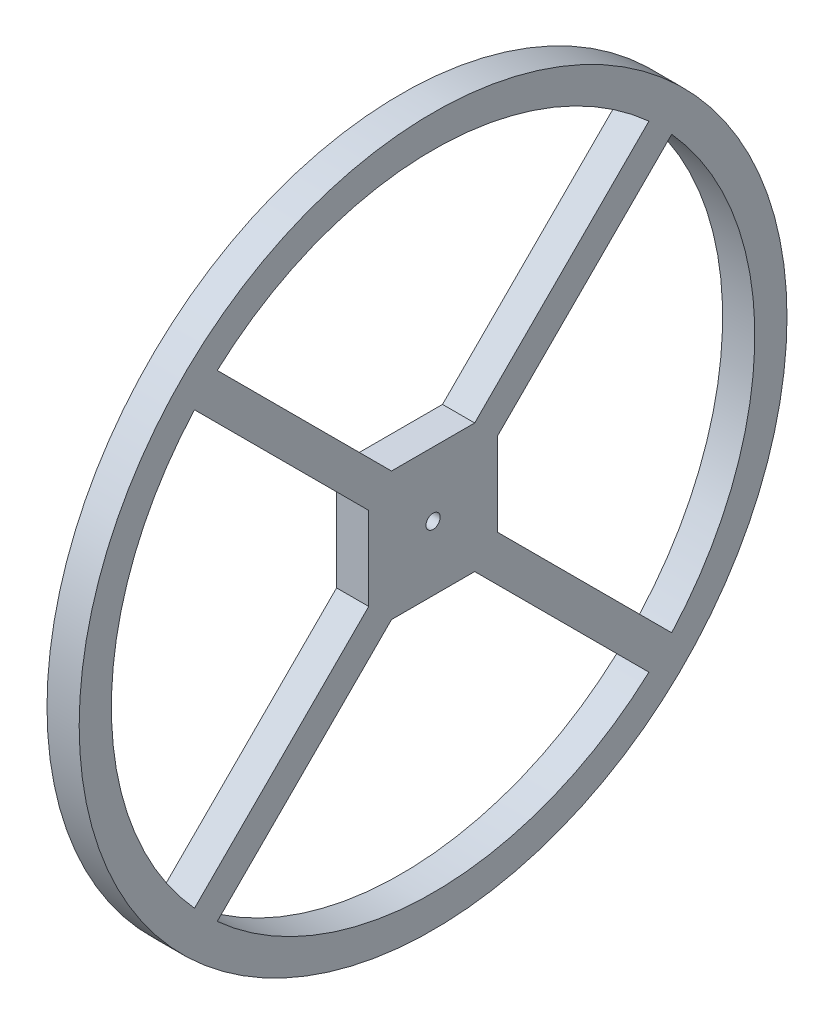
SolidWorks part; units mm, degrees
ref_plane "Front Plane" through (0, 0, 0) normal (0, 0, 1) x (1, 0, 0)
ref_plane "Top Plane" through (0, 0, 0) normal (0, 1, 0) x (1, 0, 0)
ref_plane "Right Plane" through (0, 0, 0) normal (1, 0, 0) x (0, 0, -1)
sketch "Sketch1" plane through (0, 0, 0) normal (1, 0, 0) x (0, 0, -1)
  line L0 (-4.8216, -7.65) -> (-0.6168, -3.4452)
  line L1 (-7.65, 7.65) -> (-4.8216, 7.65)
  line L2 (-7.65, 7.65) -> (-7.65, 4.8216)
  line L3 (-7.65, -7.65) -> (-4.8216, -7.65)
  line L4 (7.65, 7.65) -> (7.65, 4.8216)
  line L5 (-7.65, 7.65) -> (7.65, -7.65) construction
  line L6 (-7.65, -7.65) -> (7.65, 7.65) construction
  line L7 (-6.4645, 10) -> (6.4645, 10)
  line L8 (-10, 6.4645) -> (-10, -6.4645)
  line L9 (-6.4645, -10) -> (6.4645, -10)
  line L10 (10, 6.4645) -> (10, -6.4645)
  line L11 (-7.65, 7.65) -> (10, -10) construction
  line L12 (-10, -10) -> (10, 10) construction
  line L13 (-10, 6.4645) -> (-37.1231, 33.5876)
  line L14 (-6.4645, 10) -> (-33.5876, 37.1231)
  line L15 (-7.65, -4.8216) -> (-3.4452, -0.6168)
  line L16 (-7.65, 4.8216) -> (-3.4452, 0.6168)
  line L17 (6.4645, 10) -> (33.5876, 37.1231)
  line L18 (10, 6.4645) -> (37.1231, 33.5876)
  line L19 (10, -6.4645) -> (37.1231, -33.5876)
  line L20 (6.4645, -10) -> (33.5876, -37.1231)
  line L21 (-6.4645, -10) -> (-33.5876, -37.1231)
  line L22 (-10, -6.4645) -> (-37.1231, -33.5876)
  line L23 (-4.8216, 7.65) -> (-0.6168, 3.4452)
  line L24 (0.6168, 3.4452) -> (4.8216, 7.65)
  line L25 (-9.0642, -6.2358) -> (6.2358, 9.0642) construction
  line L26 (3.4452, 0.6168) -> (7.65, 4.8216)
  line L27 (-6.2358, -9.0642) -> (9.0642, 6.2358) construction
  line L28 (0.6168, -3.4452) -> (4.8216, -7.65)
  line L29 (-9.0642, 6.2358) -> (6.2358, -9.0642) construction
  line L30 (3.4452, -0.6168) -> (7.65, -4.8216)
  line L31 (-6.2358, 9.0642) -> (9.0642, -6.2358) construction
  line L32 (-7.65, -4.8216) -> (-7.65, -7.65)
  line L33 (4.8216, -7.65) -> (7.65, -7.65)
  line L34 (7.65, -4.8216) -> (7.65, -7.65)
  line L35 (4.8216, 7.65) -> (7.65, 7.65)
  circle A0 centre (0, 0) radius 55
  arc A1 (-37.0789, 33.5434) -> (-37.0789, -33.5434) centre (0, 0) ccw
  circle A2 centre (0, 0) radius 50 construction
  arc A3 (33.5434, 37.0789) -> (-33.5434, 37.0789) centre (0, 0) ccw
  arc A4 (-33.5434, -37.0789) -> (33.5434, -37.0789) centre (0, 0) ccw
  arc A5 (37.0789, -33.5434) -> (37.0789, 33.5434) centre (0, 0) ccw
  arc A6 (-3.4452, 0.6168) -> (-3.4452, -0.6168) centre (0, 0) ccw
  arc A7 (3.4452, -0.6168) -> (3.4452, 0.6168) centre (0, 0) ccw
  arc A8 (-0.6168, -3.4452) -> (0.6168, -3.4452) centre (0, 0) ccw
  arc A9 (0.6168, 3.4452) -> (-0.6168, 3.4452) centre (0, 0) ccw
  point P0 (0, 0)
  point P6 (0, 0)
  point P37 (0, 0)
  dimension "D5" = 110
  dimension "D7" = 7
  dimension "D1" = 15.3
  dimension "D2" = 15.3
  dimension "D3" = 20
  dimension "D4" = 20
  dimension "D6" = 5
  dimension "D8" = 2
  dimension "D10" = 2
  dimension "D11" = 2
  dimension "D12" = 2
  dimension "D9" = 4
extrude "Boss-Extrude1" add sketch "Sketch1" along normal blind 5
sketch "Sketch2" plane through (5, 0, 0) normal (1, 0, 0) x (0, 0, -1)
  line L1 (7.65, 7.65) -> (-7.65, 7.65)
  line L2 (7.65, 7.65) -> (7.65, -7.65)
  line L3 (7.65, -7.65) -> (-7.65, -7.65)
  line L4 (-7.65, 7.65) -> (-7.65, -7.65)
  line L5 (7.65, 7.65) -> (-7.65, -7.65) construction
  line L6 (7.65, -7.65) -> (-7.65, 7.65) construction
  circle A0 centre (0, 0) radius 1.1
  point P0 (0, 0)
  dimension "D1" = 2.2
extrude "Boss-Extrude2" add sketch "Sketch2" against normal blind 2
